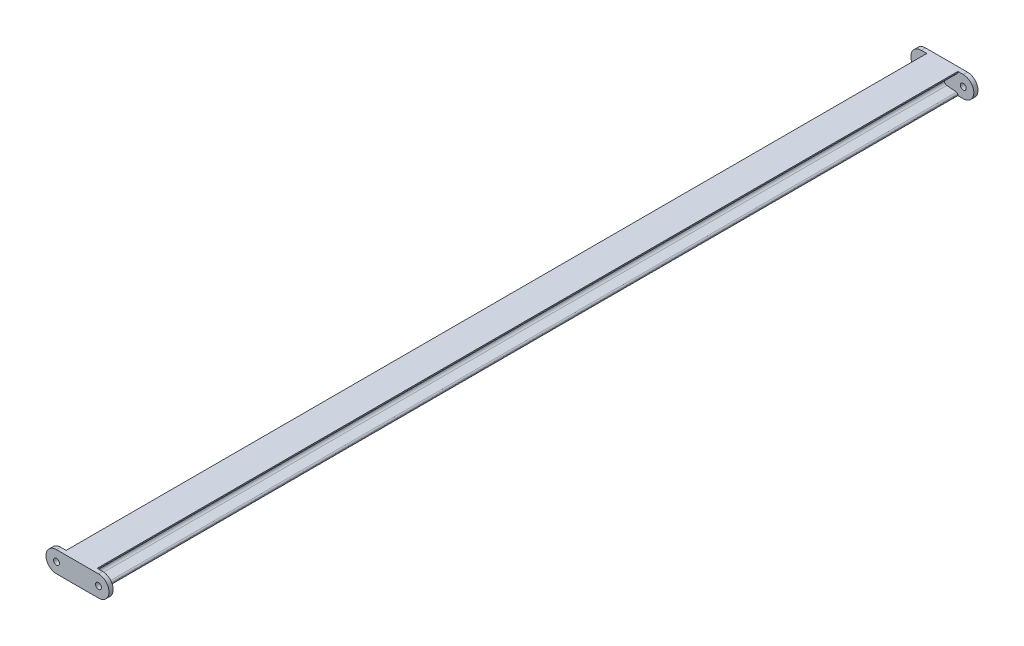
SolidWorks part; units mm, degrees
material "普通碳钢"
ref_plane "前视基准面" through (0, 0, 0) normal (0, 0, 1) x (1, 0, 0)
ref_plane "上视基准面" through (0, 0, 0) normal (0, 1, 0) x (1, 0, 0)
ref_plane "右视基准面" through (0, 0, 0) normal (1, 0, 0) x (0, 0, -1)
sketch "草图1" plane through (0, 0, 0) normal (1, 0, 0) x (0, 0, -1)
  line L0 (-1025, 0) -> (1025, 0)
  dimension "D1" = 2050
other "槽钢 5#(1)"
ref_plane "基准面1" through (0, 0, 1025) normal (0, 0, -1) x (1, 0, 0)
sketch "草图11" plane through (0, 0, 1025) normal (0, 0, -1) x (1, 0, 0)
  line L0 (0, -25) -> (37, -25)
  line L1 (37, -25) -> (37, -22.7923)
  line L2 (33.8482, -19.3097) -> (10.8035, -17.0055)
  line L3 (4.5, -10.0402) -> (4.5, 10.0402)
  line L4 (10.8035, 17.0055) -> (33.8482, 19.3097)
  line L5 (37, 22.7923) -> (37, 25)
  line L6 (37, 25) -> (0, 25)
  line L7 (0, 25) -> (0, -25)
  line L8 (20.75, 18) -> (20.75, -18) construction
  line L9 (0, 0) -> (4.5, 0) construction
  line L10 (4.5, 10.0402) -> (4.5, 35) construction
  line L11 (4.5, 35) -> (20.75, 35) construction
  line L12 (20.75, 35) -> (37, 35) construction
  line L13 (37, 35) -> (37, 25) construction
  line L14 (20.75, 35) -> (20.75, 18) construction
  arc A0 (10.8035, -17.0055) -> (4.5, -10.0402) centre (11.5, -10.0402) cw
  arc A1 (4.5, 10.0402) -> (10.8035, 17.0055) centre (11.5, 10.0402) cw
  arc A2 (37, -22.7923) -> (33.8482, -19.3097) centre (33.5, -22.7923) ccw
  arc A3 (33.8482, 19.3097) -> (37, 22.7923) centre (33.5, 22.7923) ccw
  point P2 (0, 0)
  point P19 (0, -25)
  point P20 (0, 25)
  point P22 (0, -25)
  point P23 (37, -25)
  point P24 (37, 25)
  point P26 (37, -19.6248)
  point P27 (11.5, 10.0402)
  point P28 (11.5, -10.0402)
  point P29 (37, 19.6248)
  dimension "D7" = 7
  dimension "D9" = 3.5
  dimension "D1" = 5.71
  dimension "D2" = 10
  dimension "D3" = 50
  dimension "D4" = 37
  dimension "D5" = 4.5
  dimension "D6" = 7
  dimension "D8" = 5.71
other "槽钢 5#(2)"
ref_plane "基准面2" through (0, 0, 1025) normal (0, 0, -1) x (-1, 0, 0)
sketch "草图12" plane through (0, 0, 1025) normal (0, 0, -1) x (-1, 0, 0)
  line L0 (0, -25) -> (37, -25)
  line L1 (37, -25) -> (37, -22.7923)
  line L2 (33.8482, -19.3097) -> (10.8035, -17.0055)
  line L3 (4.5, -10.0402) -> (4.5, 10.0402)
  line L4 (10.8035, 17.0055) -> (33.8482, 19.3097)
  line L5 (37, 22.7923) -> (37, 25)
  line L6 (37, 25) -> (0, 25)
  line L7 (0, 25) -> (0, -25)
  line L8 (20.75, 18) -> (20.75, -18) construction
  line L9 (0, 0) -> (4.5, 0) construction
  line L10 (4.5, 10.0402) -> (4.5, 35) construction
  line L11 (4.5, 35) -> (20.75, 35) construction
  line L12 (20.75, 35) -> (37, 35) construction
  line L13 (37, 35) -> (37, 25) construction
  line L14 (20.75, 35) -> (20.75, 18) construction
  arc A0 (10.8035, -17.0055) -> (4.5, -10.0402) centre (11.5, -10.0402) cw
  arc A1 (4.5, 10.0402) -> (10.8035, 17.0055) centre (11.5, 10.0402) cw
  arc A2 (37, -22.7923) -> (33.8482, -19.3097) centre (33.5, -22.7923) ccw
  arc A3 (33.8482, 19.3097) -> (37, 22.7923) centre (33.5, 22.7923) ccw
  point P2 (0, 0)
  point P19 (0, -25)
  point P20 (0, 25)
  point P22 (0, -25)
  point P23 (37, -25)
  point P24 (37, 25)
  point P26 (37, -19.6248)
  point P27 (11.5, 10.0402)
  point P28 (11.5, -10.0402)
  point P29 (37, 19.6248)
  dimension "D7" = 7
  dimension "D9" = 3.5
  dimension "D1" = 5.71
  dimension "D2" = 10
  dimension "D3" = 50
  dimension "D4" = 37
  dimension "D5" = 4.5
  dimension "D6" = 7
  dimension "D8" = 5.71
sketch "草图13" plane through (0, 0, 1025) normal (0, 0, 1) x (1, 0, 0)
  line L0 (0, -25) -> (0, 25) construction
  line L5 (37, -25) -> (0, -25) construction
  line L6 (0, -25) -> (-37, -25) construction
  line L7 (-37, 25) -> (0, 25) construction
  line L8 (0, 25) -> (37, 25) construction
  line L9 (50, -25) -> (0, -25)
  line L10 (0, -25) -> (-50, -25)
  line L11 (-50, 25) -> (0, 25)
  line L12 (0, 25) -> (50, 25)
  line L13 (-50, 25) -> (-50, -25) construction
  line L14 (50, 25) -> (50, -25) construction
  line L15 (0, 25) -> (0, -25) construction
  arc A2 (-50, 25) -> (-50, -25) centre (-50, 0) ccw
  arc A3 (50, -25) -> (50, 25) centre (50, 0) ccw
  dimension "D1" = 50
  dimension "D2" = 50
extrude "凸台-拉伸1" add sketch "草图13" along normal blind 10 contours A2 L10 L9 A3 L12 L11
sketch "草图14" plane through (0, 0, 1035) normal (0, 0, 1) x (1, 0, 0)
  circle A0 centre (-50, 0) radius 7
  circle A1 centre (50, 0) radius 7
  dimension "D1" = 14
  dimension "D2" = 14
extrude "切除-拉伸1" cut sketch "草图14" against normal blind 10
mirror "镜向4" about plane through (0, 0, 0) normal (0, 0, 1) of "切除-拉伸1", "凸台-拉伸1"
